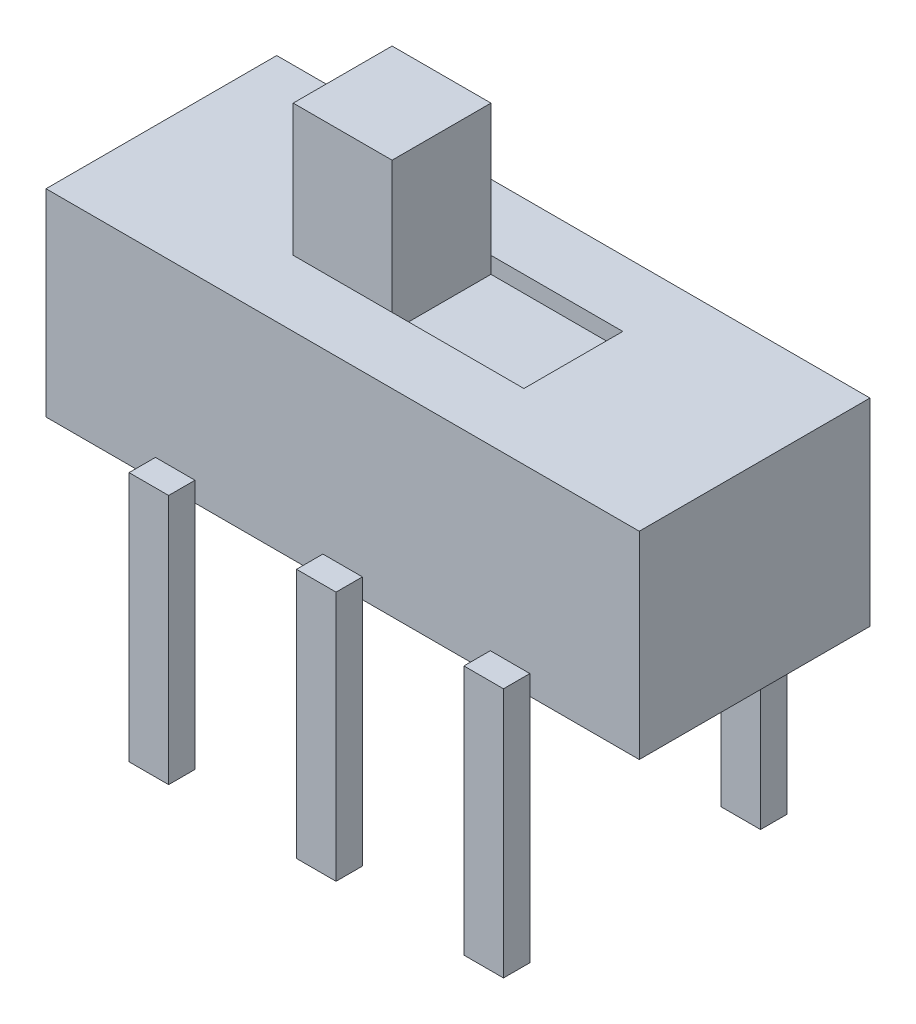
SolidWorks part; units mm, degrees
ref_plane "Plan de face" through (0, 0, 0) normal (0, 0, 1) x (1, 0, 0)
ref_plane "Plan de dessus" through (0, 0, 0) normal (0, 1, 0) x (1, 0, 0)
ref_plane "Plan de droite" through (0, 0, 0) normal (1, 0, 0) x (0, 0, -1)
sketch "Esquisse1" plane through (0, 0, 0) normal (0, 1, 0) x (1, 0, 0)
  line L1 (-4.5, -1.75) -> (4.5, -1.75)
  line L2 (-4.5, -1.75) -> (-4.5, 1.75)
  line L3 (-4.5, 1.75) -> (4.5, 1.75)
  line L4 (4.5, -1.75) -> (4.5, 1.75)
  line L5 (-4.5, -1.75) -> (4.5, 1.75) construction
  line L6 (-4.5, 1.75) -> (4.5, -1.75) construction
  point P0 (0, 0)
  dimension "D1" = 9
  dimension "D2" = 3.5
extrude "Boss.-Extru.1" add sketch "Esquisse1" along normal blind 3
sketch "Esquisse2" plane through (0, 3, 0) normal (0, 1, 0) x (1, 0, 0)
  line L1 (-1.75, -0.75) -> (-0.25, -0.75)
  line L2 (-1.75, -0.75) -> (-1.75, 0.75)
  line L3 (-1.75, 0.75) -> (-0.25, 0.75)
  line L4 (-0.25, -0.75) -> (-0.25, 0.75)
  line L5 (-1.75, -0.75) -> (-0.25, 0.75) construction
  line L6 (-1.75, 0.75) -> (-0.25, -0.75) construction
  point P0 (-1, 0)
  dimension "D1" = 1.5
  dimension "D2" = 0.25
extrude "Boss.-Extru.2" add sketch "Esquisse2" along normal blind 2
sketch "Esquisse3" plane through (0, 3, 0) normal (0, 1, 0) x (1, 0, 0)
  line L0 (-1.75, -0.75) -> (-0.25, -0.75) construction
  line L1 (-0.25, 0.75) -> (1.75, 0.75)
  line L2 (-0.25, 0.75) -> (-0.25, -0.75)
  line L3 (-0.25, -0.75) -> (1.75, -0.75)
  line L4 (1.75, 0.75) -> (1.75, -0.75)
  dimension "D1" = 2
extrude "Enlèv. mat.-Extru.1" cut sketch "Esquisse3" against normal blind 0.25
sketch "Esquisse4" plane through (0, 0, 1.75) normal (0, 0, 1) x (1, 0, 0)
  line L0 (-4.5, 0) -> (4.5, 0) construction
  line L1 (-2.84, 0.3) -> (-2.24, 0.3)
  line L2 (-2.84, 0.3) -> (-2.84, -3.5)
  line L3 (-2.84, -3.5) -> (-2.24, -3.5)
  line L4 (-2.24, 0.3) -> (-2.24, -3.5)
  point P4 (0, 0)
  dimension "D1" = 0.6
  dimension "D2" = 2.24
  dimension "D3" = 0.3
  dimension "D4" = 3.5
extrude "Boss.-Extru.3" add sketch "Esquisse4" along normal blind 0.4 separate body
pattern_linear "Répétition linéaire1" count 3 spacing 2.54 along (1, 0, 0) of bodies 104
mirror "Symétrie1" about plane through (0, 0, 0) normal (0, 0, 1) of bodies 104 105 106
